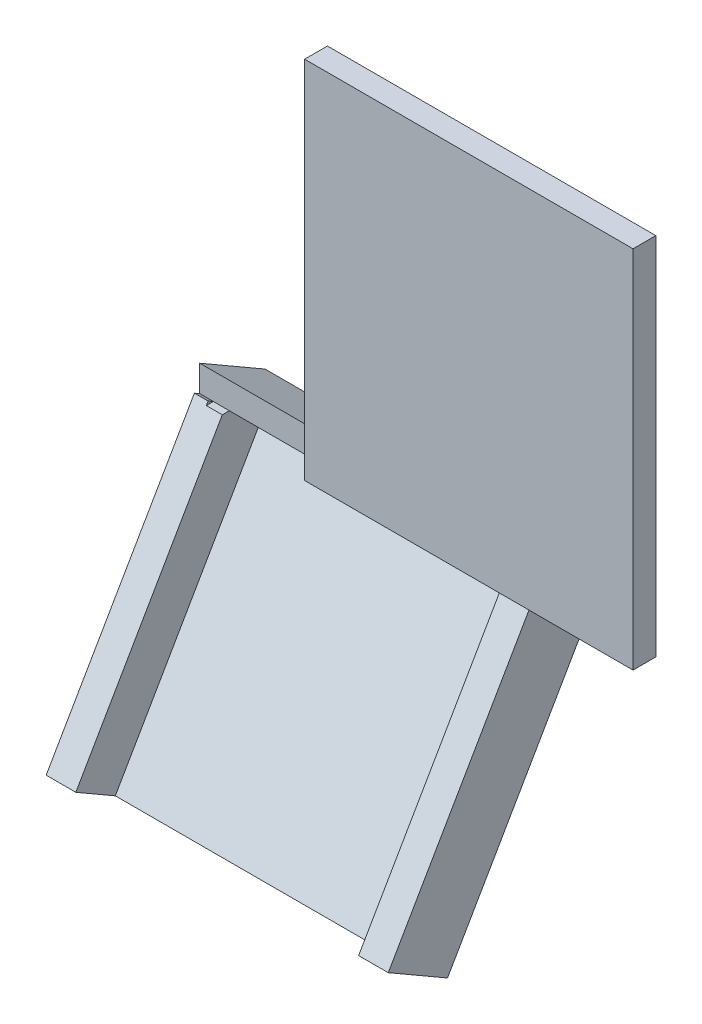
SolidWorks part; units mm, degrees
material "ABS"
ref_plane "Ebene vorne" through (0, 0, 0) normal (0, 0, 1) x (1, 0, 0)
ref_plane "Ebene oben" through (0, 0, 0) normal (0, 1, 0) x (1, 0, 0)
ref_plane "Ebene rechts" through (0, 0, 0) normal (1, 0, 0) x (0, 0, -1)
sketch "Skizze1" plane through (0, 0, 0) normal (0, 0, 1) x (1, 0, 0)
  line L1 (0, 0) -> (14.4, 0)
  line L2 (0, 0) -> (0, 16)
  line L3 (0, 16) -> (14.4, 16)
  line L4 (14.4, 0) -> (14.4, 16)
  dimension "D1" = 14.4
  dimension "D2" = 16
extrude "Aufsatz-Linear austragen1" add sketch "Skizze1" along normal blind 1
sketch "Skizze4" plane through (14.4, 0, 0) normal (1, 0, 0) x (0, 0, -1)
  line L0 (-1, 0) -> (2, 0) construction
  line L1 (2, 0) -> (0, 1.1547)
  line L2 (0, 0) -> (0, 16) construction
  line L3 (2, 0) -> (-5, -12.1244)
  line L4 (2, 0) -> (2.866, -0.5)
  line L5 (2.866, -0.5) -> (-4.134, -12.6244)
  line L6 (-4.134, -12.6244) -> (-5, -12.1244)
  line L7 (1.5, -0.866) -> (0, 0)
  dimension "D1" = 1
  dimension "D2" = 14
  dimension "D3" = 30
  dimension "D4" = 14
  dimension "D5" = 3
  dimension "D6" = 1
extrude "Aufsatz-Linear austragen4" add sketch "Skizze4" against normal blind 15
sketch "Skizze9" plane through (0, -0.866, -1.5) normal (0, 0.5, 0.866) x (1, 0, 0)
  line L0 (-0.6, -13) -> (14.4, -13) construction
  line L1 (14.4, 0) -> (13.1, 0)
  line L2 (14.4, 0) -> (14.4, -13)
  line L3 (14.4, -13) -> (13.1, -13)
  line L4 (13.1, 0) -> (13.1, -13)
  line L7 (-0.6, 0) -> (0.7, 0)
  line L9 (-0.6, 0) -> (-0.6, -13)
  line L10 (-0.6, -13) -> (0.7, -13)
  line L11 (0.7, 0) -> (0.7, -13)
  dimension "D1" = 1.3
  dimension "D2" = 1.3
extrude "Aufsatz-Linear austragen5" add sketch "Skizze9" along normal blind 2
sketch "Skizze10" plane through (14.4, 0, 0) normal (1, 0, 0) x (0, 0, -1)
  line L1 (-1, 16) -> (0, 16)
  line L2 (-1, 16) -> (-1, 0)
  line L3 (-1, 0) -> (0, 0)
  line L4 (0, 16) -> (0, 0)
extrude "Aufsatz-Linear austragen6" add sketch "Skizze10" along normal blind 5
sketch "Skizze13" plane through (0, 0, 0) normal (-1, 0, 0) x (0, 0, 1)
  line L1 (0, 16) -> (1, 16)
  line L2 (0, 16) -> (0, 0)
  line L3 (0, 0) -> (1, 0)
  line L4 (1, 16) -> (1, 0)
extrude "Schnitt-Linear austragen4" cut sketch "Skizze13" against normal blind 5
